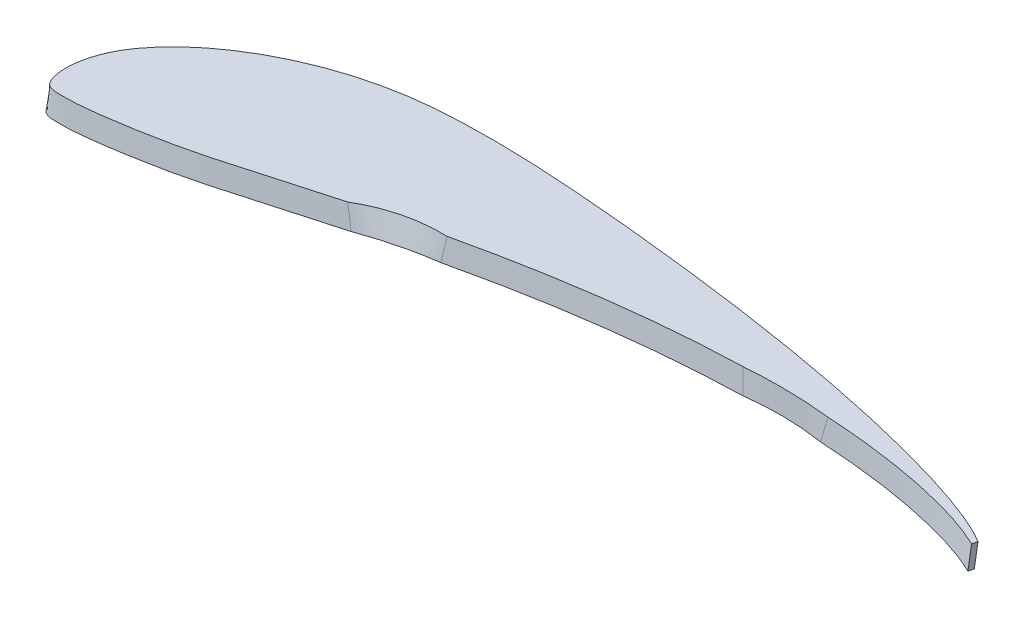
SolidWorks part; units mm, degrees
material "Elastyczna pianka poliuretanowa"
ref_plane "Płaszczyzna XY" through (0, 0, 0) normal (0, 0, 1) x (1, 0, 0)
ref_plane "Płaszczyzna XZ" through (0, 0, 0) normal (0, 1, 0) x (1, 0, 0)
ref_plane "Płaszczyzna YZ" through (0, 0, 0) normal (1, 0, 0) x (0, 0, -1)
sketch "Szkic1" plane through (0, 250.3609, 48.6652) normal (0, -0.9816, -0.1908) x (1, 0, 0)
  line L5 (-466.8113, 187.1171) -> (-472.9601, 210.044)
  line L6 (-486.589, 213.3723) -> (-503.6753, 194.6998)
  line L7 (-230.7182, 186.7181) -> (-231.6453, 188.6919)
  line L8 (-309.7858, 174.2461) -> (-322.6938, 197.9387)
  line L9 (-336.9508, 197.5316) -> (-348.183, 173.7817)
  line L12 (-230.7182, 186.7181) -> (-231.6453, 188.6919)
  arc A2 (-472.9601, 210.044) -> (-486.589, 213.3723) centre (-480.687, 207.9716) ccw
  arc A3 (-322.6938, 197.9387) -> (-336.9508, 197.5316) centre (-329.7188, 194.1114) ccw
  spline S0 degree 2 poles (-503.6753, 194.6998) (-486.1131, 186.6285) (-466.8113, 187.1171) knots 0 0 0 1 1 1
  spline S1 degree 2 poles (-348.183, 173.7817) (-328.9642, 172.457) (-309.7858, 174.2461) knots 0 0 0 1 1 1
  spline S3 degree 3 poles (961.1071, 2784.9605) (376.8727, 422.5481) (-14.446, 148.7113) (-387.9442, 175.9711) (-397.8476, 176.9178) (-417.6182, 179.2031) (-427.4849, 180.547) (-442.2607, 182.8262) (-447.1833, 183.629) (-952.66, 270.3189) (-1365.321, 774.2281) (-2411.9455, -1736.9733) knots -8.909011 -8.909011 -8.909011 -8.909011 0.25 0.25 0.5 0.5 0.75 0.75 0.875 0.875 13.61022 13.61022 13.61022 13.61022 only from (-348.183, 173.7817) to (-466.8113, 187.1171)
  spline S4 degree 3 poles (959.8042, 2726.3226) (76.9137, 59.3384) (-230.2357, 130.5607) (-542.8432, 203.7255) (-548.4338, 205.0452) (-556.8474, 206.8622) (-559.6562, 207.4413) (-565.2857, 208.5257) (-568.1069, 209.0278) (-573.7585, 209.9746) (-576.5885, 210.422) (-582.2554, 211.2742) (-585.0925, 211.6778) (-590.7758, 212.4276) (-593.6225, 212.7716) (-597.9026, 213.2244) (-599.3309, 213.3652) (-602.191, 213.626) (-603.6218, 213.7485) (-605.7691, 213.8905) (-606.485, 213.9308) (-607.9176, 213.9915) (-608.6343, 214.0112) (-610.0682, 214.0317) (-610.7855, 214.0332) (-612.2204, 214.0255) (-612.9379, 214.0186) (-614.3734, 213.9904) (-615.0944, 213.9596) (-616.1543, 213.8006) (-616.5044, 213.729) (-617.1963, 213.5371) (-617.5399, 213.4171) (-618.0259, 213.187) (-618.1836, 213.1018) (-618.4876, 212.9093) (-618.6352, 212.8007) (-618.9052, 212.5631) (-619.0284, 212.4336) (-619.2483, 212.1509) (-619.3465, 211.9965) (-619.6026, 211.5197) (-619.7252, 211.185) (-619.9226, 210.4991) (-619.9974, 210.1467) (-620.1221, 209.4394) (-620.17, 209.0839) (-620.2369, 208.3694) (-620.2561, 208.0094) (-620.2723, 206.9367) (-620.229, 206.2281) (-620.0607, 204.8205) (-619.9359, 204.1216) (-619.6245, 202.7312) (-619.4375, 202.0389) (-618.8007, 200.0009) (-618.2741, 198.6833) (-617.0617, 196.1121) (-616.374, 194.855) (-614.892, 192.4402) (-614.0928, 191.278) (-612.3839, 189.0391) (-611.4752, 187.9617) (-610.0457, 186.3971) (-609.558, 185.8842) (-608.5628, 184.8738) (-608.0543, 184.3755) (-606.5106, 182.909) (-605.4579, 181.9682) (-602.2469, 179.2284) (-600.0321, 177.5176) (-595.481, 174.2855) (-593.1452, 172.7635) (-588.3746, 169.874) (-585.94, 168.5062) (-580.9833, 165.9072) (-578.4601, 164.6778) (-574.6136, 162.9297) (-573.3212, 162.3628) (-570.7287, 161.2633) (-569.4273, 160.7298) (-565.5081, 159.1767) (-562.8751, 158.2045) (-557.5706, 156.3815) (-554.8991, 155.5304) (-549.5196, 153.9429) (-546.8116, 153.2068) (-542.7197, 152.1962) (-541.3507, 151.8751) (-538.6028, 151.2642) (-537.2227, 150.9739) (-533.0776, 150.1498) (-530.3121, 149.6617) (-524.7767, 148.8025) (-522.0069, 148.4327) (-516.4629, 147.8151) (-513.6887, 147.5661) (-505.3607, 146.9725) (-499.8012, 146.7859) (-488.6755, 146.5949) (-483.1089, 146.6035) (-471.9685, 146.8235) (-466.3949, 147.0264) (-455.2431, 147.5596) (-449.6626, 147.892) (-438.5168, 148.644) (-432.9494, 149.0616) (-421.8235, 149.9646) (-416.2651, 150.4506) (-405.1554, 151.4766) (-399.6041, 152.0165) (-382.9635, 153.7375) (-371.8875, 155.019) (-355.3036, 157.1703) (-349.7809, 157.9278) (-338.7475, 159.5325) (-333.2363, 160.3771) (-322.2269, 162.1645) (-316.7289, 163.1091) (-305.7473, 165.108) (-300.2637, 166.1621) (-292.0521, 167.8474) (-289.3172, 168.4267) (-283.8526, 169.625) (-281.1218, 170.2445) (-272.9497, 172.17) (-267.527, 173.5404) (-259.4493, 175.7889) (-256.7663, 176.5713) (-251.4259, 178.2236) (-248.7682, 179.0926) (-244.809, 180.4894) (-243.4939, 180.9709) (-240.875, 181.9727) (-239.5705, 182.4936) (-236.9854, 183.5816) (-235.7024, 184.1461) (-176.5919, 212.4643) (-159.7166, 327.3712) (-1332.0236, 2973.0527) knots -1.653404 -1.653404 -1.653404 -1.653404 0.0625 0.0625 0.09375 0.09375 0.109375 0.109375 0.125 0.125 0.140625 0.140625 0.15625 0.15625 0.171875 0.171875 0.179687 0.179687 0.1875 0.1875 0.191406 0.191406 0.195312 0.195312 0.199219 0.199219 0.203125 0.203125 0.207031 0.207031 0.208984 0.208984 0.210937 0.210937 0.211914 0.211914 0.212891 0.212891 0.213867 0.213867 0.214844 0.214844 0.216797 0.216797 0.21875 0.21875 0.220703 0.220703 0.222656 0.222656 0.226562 0.226562 0.230469 0.230469 0.234375 0.234375 0.242187 0.242187 0.25 0.25 0.257812 0.257812 0.265625 0.265625 0.269531 0.269531 0.273437 0.273437 0.28125 0.28125 0.296875 0.296875 0.3125 0.3125 0.328125 0.328125 0.34375 0.34375 0.351562 0.351562 0.359375 0.359375 0.375 0.375 0.390625 0.390625 0.40625 0.40625 0.414062 0.414062 0.421875 0.421875 0.4375 0.4375 0.453125 0.453125 0.46875 0.46875 0.5 0.5 0.53125 0.53125 0.5625 0.5625 0.59375 0.59375 0.625 0.625 0.65625 0.65625 0.6875 0.6875 0.75 0.75 0.78125 0.78125 0.8125 0.8125 0.84375 0.84375 0.875 0.875 0.890625 0.890625 0.90625 0.90625 0.9375 0.9375 0.953125 0.953125 0.96875 0.96875 0.976562 0.976562 0.984375 0.984375 0.992187 0.992187 1.349806 1.349806 1.349806 1.349806 only from (-503.6753, 194.6998) to (-230.7182, 186.7181)
  spline S5 degree 3 poles (-883.9723, 3110.6661) (-105.8224, 363.0378) (-153.1749, 218.5298) (-237.8412, 186.1719) (-239.414, 185.617) (-244.1644, 184.0531) (-247.3745, 183.1467) (-253.8516, 181.5134) (-257.1199, 180.7803) (-263.6577, 179.4539) (-266.9328, 178.8602) (-276.7736, 177.253) (-283.3547, 176.4124) (-650.9504, 139.297) (-1058.5112, 625.3856) (-1139.4136, -2554.4342) knots -3.267662 -3.267662 -3.267662 -3.267662 0.0625 0.0625 0.125 0.125 0.25 0.25 0.375 0.375 0.5 0.5 0.75 0.75 14.431103 14.431103 14.431103 14.431103 only from (-231.6453, 188.6919) to (-309.7858, 174.2461)
  spline S6 degree 3 poles (-348.183, 173.7817) (-358.1517, 174.022) (-368.0963, 174.5225) (-387.9442, 175.9711) (-397.8476, 176.9178) (-417.6182, 179.2031) (-427.4849, 180.547) (-442.2607, 182.8262) (-447.1833, 183.629) (-457.0097, 185.3143) (-461.9144, 186.1972) (-466.8113, 187.1171) knots 0 0 0 0 0.25 0.25 0.5 0.5 0.75 0.75 0.875 0.875 1 1 1 1
  spline S7 degree 3 poles (-503.6753, 194.6998) (-514.8862, 197.1832) (-526.0691, 199.7996) (-542.8432, 203.7255) (-548.4338, 205.0452) (-556.8474, 206.8622) (-559.6562, 207.4413) (-565.2857, 208.5257) (-568.1069, 209.0278) (-573.7585, 209.9746) (-576.5885, 210.422) (-582.2554, 211.2742) (-585.0925, 211.6778) (-590.7758, 212.4276) (-593.6225, 212.7716) (-597.9026, 213.2244) (-599.3309, 213.3652) (-602.191, 213.626) (-603.6218, 213.7485) (-605.7691, 213.8905) (-606.485, 213.9308) (-607.9176, 213.9915) (-608.6343, 214.0112) (-610.0682, 214.0317) (-610.7855, 214.0332) (-612.2204, 214.0255) (-612.9379, 214.0186) (-614.3734, 213.9904) (-615.0944, 213.9596) (-616.1543, 213.8006) (-616.5044, 213.729) (-617.1963, 213.5371) (-617.5399, 213.4171) (-618.0259, 213.187) (-618.1836, 213.1018) (-618.4876, 212.9093) (-618.6352, 212.8007) (-618.9052, 212.5631) (-619.0284, 212.4336) (-619.2483, 212.1509) (-619.3465, 211.9965) (-619.6026, 211.5197) (-619.7252, 211.185) (-619.9226, 210.4991) (-619.9974, 210.1467) (-620.1221, 209.4394) (-620.17, 209.0839) (-620.2369, 208.3694) (-620.2561, 208.0094) (-620.2723, 206.9367) (-620.229, 206.2281) (-620.0607, 204.8205) (-619.9359, 204.1216) (-619.6245, 202.7312) (-619.4375, 202.0389) (-618.8007, 200.0009) (-618.2741, 198.6833) (-617.0617, 196.1121) (-616.374, 194.855) (-614.892, 192.4402) (-614.0928, 191.278) (-612.3839, 189.0391) (-611.4752, 187.9617) (-610.0457, 186.3971) (-609.558, 185.8842) (-608.5628, 184.8738) (-608.0543, 184.3755) (-606.5106, 182.909) (-605.4579, 181.9682) (-602.2469, 179.2284) (-600.0321, 177.5176) (-595.481, 174.2855) (-593.1452, 172.7635) (-588.3746, 169.874) (-585.94, 168.5062) (-580.9833, 165.9072) (-578.4601, 164.6778) (-574.6136, 162.9297) (-573.3212, 162.3628) (-570.7287, 161.2633) (-569.4273, 160.7298) (-565.5081, 159.1767) (-562.8751, 158.2045) (-557.5706, 156.3815) (-554.8991, 155.5304) (-549.5196, 153.9429) (-546.8116, 153.2068) (-542.7197, 152.1962) (-541.3507, 151.8751) (-538.6028, 151.2642) (-537.2227, 150.9739) (-533.0776, 150.1498) (-530.3121, 149.6617) (-524.7767, 148.8025) (-522.0069, 148.4327) (-516.4629, 147.8151) (-513.6887, 147.5661) (-505.3607, 146.9725) (-499.8012, 146.7859) (-488.6755, 146.5949) (-483.1089, 146.6035) (-471.9685, 146.8235) (-466.3949, 147.0264) (-455.2431, 147.5596) (-449.6626, 147.892) (-438.5168, 148.644) (-432.9494, 149.0616) (-421.8235, 149.9646) (-416.2651, 150.4506) (-405.1554, 151.4766) (-399.6041, 152.0165) (-382.9635, 153.7375) (-371.8875, 155.019) (-355.3036, 157.1703) (-349.7809, 157.9278) (-338.7475, 159.5325) (-333.2363, 160.3771) (-322.2269, 162.1645) (-316.7289, 163.1091) (-305.7473, 165.108) (-300.2637, 166.1621) (-292.0521, 167.8474) (-289.3172, 168.4267) (-283.8526, 169.625) (-281.1218, 170.2445) (-272.9497, 172.17) (-267.527, 173.5404) (-259.4493, 175.7889) (-256.7663, 176.5713) (-251.4259, 178.2236) (-248.7682, 179.0926) (-244.809, 180.4894) (-243.4939, 180.9709) (-240.875, 181.9727) (-239.5705, 182.4936) (-236.9854, 183.5816) (-235.7024, 184.1461) (-233.175, 185.3569) (-231.9308, 186.004) (-230.7182, 186.7181) knots 0 0 0 0 0.0625 0.0625 0.09375 0.09375 0.109375 0.109375 0.125 0.125 0.140625 0.140625 0.15625 0.15625 0.171875 0.171875 0.179687 0.179687 0.1875 0.1875 0.191406 0.191406 0.195312 0.195312 0.199219 0.199219 0.203125 0.203125 0.207031 0.207031 0.208984 0.208984 0.210937 0.210937 0.211914 0.211914 0.212891 0.212891 0.213867 0.213867 0.214844 0.214844 0.216797 0.216797 0.21875 0.21875 0.220703 0.220703 0.222656 0.222656 0.226562 0.226562 0.230469 0.230469 0.234375 0.234375 0.242187 0.242187 0.25 0.25 0.257812 0.257812 0.265625 0.265625 0.269531 0.269531 0.273437 0.273437 0.28125 0.28125 0.296875 0.296875 0.3125 0.3125 0.328125 0.328125 0.34375 0.34375 0.351562 0.351562 0.359375 0.359375 0.375 0.375 0.390625 0.390625 0.40625 0.40625 0.414062 0.414062 0.421875 0.421875 0.4375 0.4375 0.453125 0.453125 0.46875 0.46875 0.5 0.5 0.53125 0.53125 0.5625 0.5625 0.59375 0.59375 0.625 0.625 0.65625 0.65625 0.6875 0.6875 0.75 0.75 0.78125 0.78125 0.8125 0.8125 0.84375 0.84375 0.875 0.875 0.890625 0.890625 0.90625 0.90625 0.9375 0.9375 0.953125 0.953125 0.96875 0.96875 0.976562 0.976562 0.984375 0.984375 0.992187 0.992187 1 1 1 1
  spline S8 degree 3 poles (-231.6453, 188.6919) (-233.1746, 188) (-234.7218, 187.3641) (-237.8412, 186.1719) (-239.414, 185.617) (-244.1644, 184.0531) (-247.3745, 183.1467) (-253.8516, 181.5134) (-257.1199, 180.7803) (-263.6577, 179.4539) (-266.9328, 178.8602) (-276.7736, 177.253) (-283.3547, 176.4124) (-296.5481, 175.0803) (-303.1603, 174.5888) (-309.7858, 174.2461) knots 0 0 0 0 0.0625 0.0625 0.125 0.125 0.25 0.25 0.375 0.375 0.5 0.5 0.75 0.75 1 1 1 1
  dimension "D1" = 0
sketch "Szkic2" plane through (0, 241.3299, 46.9098) normal (0, 0.9816, 0.1908) x (1, 0, 0)
  line L5 (-346.5635, -177.2061) -> (-336.9508, -197.5316)
  line L6 (-322.6938, -197.9387) -> (-311.6218, -177.6162)
  line L7 (-231.6462, -192.1508) -> (-230.7191, -190.1773)
  line L8 (-501.0426, -197.5769) -> (-486.589, -213.3723)
  line L9 (-472.9601, -210.044) -> (-467.7883, -190.76)
  line L12 (-231.6462, -192.1508) -> (-230.7191, -190.1773)
  arc A2 (-336.9508, -197.5316) -> (-322.6938, -197.9387) centre (-329.7188, -194.1114) ccw
  arc A3 (-486.589, -213.3723) -> (-472.9601, -210.044) centre (-480.687, -207.9716) ccw
  spline S0 degree 2 poles (-501.0426, -197.5769) (-484.7064, -192.7356) (-467.7883, -190.76) knots 0 0 0 1 1 1
  spline S1 degree 2 poles (-346.5635, -177.2061) (-329.0621, -175.2488) (-311.6218, -177.6162) knots 0 0 0 1 1 1
  spline S3 degree 3 poles (-2391.9418, 1769.2386) (-1351.11, -759.7133) (-944.2235, -272.689) (-447.74, -187.1805) (-442.7129, -186.3578) (-427.6223, -184.0241) (-417.543, -182.6508) (-397.3413, -180.324) (-387.2194, -179.3651) (-372.0005, -178.2765) (-366.9215, -177.9724) (-59.4889, -163.4322) (280.3775, -373.7296) (-2743.4147, -1900.722) knots -12.116321 -12.116321 -12.116321 -12.116321 0.125 0.125 0.25 0.25 0.5 0.5 0.75 0.75 0.875 0.875 8.306481 8.306481 8.306481 8.306481 only from (-467.7883, -190.76) to (-346.5635, -177.2061)
  spline S4 degree 3 poles (-1192.0704, 2530.1655) (-1065.4952, -639.2296) (-658.0587, -143.4351) (-284.5996, -179.7248) (-277.8676, -180.5599) (-267.797, -182.1697) (-264.4447, -182.7664) (-259.4246, -183.769) (-257.7526, -184.1214) (-254.4117, -184.8663) (-252.7433, -185.2585) (-247.7636, -186.4999) (-244.473, -187.4191) (-239.6047, -189.0104) (-237.9931, -189.5759) (-152.8386, -221.9932) (-105.2977, -366.946) (-885.8816, -3113.4705) knots -13.340567 -13.340567 -13.340567 -13.340567 0.25 0.25 0.5 0.5 0.625 0.625 0.6875 0.6875 0.75 0.75 0.875 0.875 0.9375 0.9375 4.205555 4.205555 4.205555 4.205555 only from (-311.6218, -177.6162) to (-231.6462, -192.1508)
  spline S5 degree 3 poles (-1667.1028, -2818.5437) (-146.9055, -333.2023) (-177.4327, -215.465) (-235.7553, -187.582) (-237.0435, -187.0164) (-240.9306, -185.3834) (-243.5556, -184.3908) (-248.8479, -182.5265) (-251.5154, -181.6556) (-256.8801, -179.9984) (-259.5776, -179.2131) (-264.9955, -177.7078) (-267.7169, -176.9877) (-273.1732, -175.6001) (-275.9055, -174.9339) (-284.1129, -173.0045) (-289.5984, -171.8105) (-300.5904, -169.5602) (-306.0969, -168.5043) (-317.1264, -166.502) (-322.6495, -165.5559) (-339.242, -162.8707) (-350.3327, -161.2725) (-372.5633, -158.4009) (-383.7018, -157.1184) (-400.4402, -155.3973) (-406.0248, -154.8572) (-417.2021, -153.8311) (-422.7965, -153.3456) (-433.9862, -152.446) (-439.5814, -152.0308) (-450.7728, -151.2874) (-456.369, -150.9616) (-467.563, -150.4446) (-473.1607, -150.2514) (-484.3582, -150.0585) (-489.9582, -150.0667) (-501.1604, -150.2911) (-506.7627, -150.5044) (-515.1698, -151.1586) (-517.9728, -151.4304) (-523.5802, -152.1007) (-526.3878, -152.4995) (-534.7407, -153.8667) (-540.2408, -155.0033) (-548.3749, -157.0894) (-551.0677, -157.8458) (-556.4186, -159.4725) (-559.0764, -160.3437) (-564.3549, -162.2081) (-566.9755, -163.2015) (-572.1778, -165.3161) (-574.76, -166.4359) (-579.879, -168.8239) (-582.4215, -170.0967) (-587.4, -172.7806) (-589.8423, -174.1921) (-597.0062, -178.6685) (-601.5674, -181.9712) (-606.8662, -186.6968) (-607.9073, -187.675) (-609.9066, -189.6896) (-610.8675, -190.7281) (-612.693, -192.8826) (-613.5572, -193.9988) (-614.7672, -195.7426) (-615.1565, -196.3351) (-615.9062, -197.5435) (-616.2672, -198.1604) (-617.3012, -200.0402) (-617.9189, -201.3214) (-618.9757, -203.9529) (-619.4154, -205.3032) (-619.901, -207.3961) (-620.0336, -208.1038) (-620.216, -209.5188) (-620.2918, -210.5842) (-620.248, -211.6578) (-620.1896, -212.3755) (-620.1458, -212.734) (-620.0297, -213.4422) (-619.9597, -213.7937) (-619.822, -214.3136) (-619.7703, -214.4856) (-619.6499, -214.8258) (-619.5807, -214.9953) (-619.4218, -215.3205) (-619.3321, -215.4767) (-619.1259, -215.7721) (-619.0071, -215.9122) (-618.6148, -216.2918) (-618.3125, -216.492) (-617.6633, -216.8221) (-617.326, -216.9474) (-616.6364, -217.1515) (-616.283, -217.2297) (-615.2099, -217.4043) (-614.4867, -217.4399) (-613.4013, -217.4639) (-613.0398, -217.468) (-612.3167, -217.4768) (-611.9552, -217.4803) (-610.1482, -217.4911) (-608.7043, -217.4773) (-605.8228, -217.3573) (-604.3848, -217.2573) (-601.5114, -217.0217) (-600.0758, -216.8894) (-597.2057, -216.6069) (-595.7713, -216.4552) (-591.4705, -215.9695) (-588.6054, -215.6043) (-582.8872, -214.82) (-580.0329, -214.4016) (-574.3326, -213.5197) (-571.4861, -213.0585) (-565.8046, -212.0736) (-562.9702, -211.5463) (-557.3151, -210.4166) (-554.4938, -209.8175) (-548.86, -208.5717) (-546.0473, -207.9254) (-540.4248, -206.6174) (-537.6147, -205.9576) (-227.5539, -133.4405) (81.3517, -69.4561) (962.8198, -2729.4203) knots -0.342252 -0.342252 -0.342252 -0.342252 0.007812 0.007812 0.015625 0.015625 0.03125 0.03125 0.046875 0.046875 0.0625 0.0625 0.078125 0.078125 0.09375 0.09375 0.125 0.125 0.15625 0.15625 0.1875 0.1875 0.25 0.25 0.3125 0.3125 0.34375 0.34375 0.375 0.375 0.40625 0.40625 0.4375 0.4375 0.46875 0.46875 0.5 0.5 0.53125 0.53125 0.546875 0.546875 0.5625 0.5625 0.59375 0.59375 0.609375 0.609375 0.625 0.625 0.640625 0.640625 0.65625 0.65625 0.671875 0.671875 0.6875 0.6875 0.71875 0.71875 0.726562 0.726562 0.734375 0.734375 0.742187 0.742187 0.746094 0.746094 0.75 0.75 0.757812 0.757812 0.765625 0.765625 0.769531 0.769531 0.773437 0.775391 0.775391 0.777344 0.777344 0.779297 0.779297 0.780273 0.780273 0.78125 0.78125 0.782227 0.782227 0.783203 0.783203 0.785156 0.785156 0.787109 0.787109 0.789062 0.789062 0.792969 0.792969 0.794922 0.794922 0.796875 0.796875 0.804687 0.804687 0.8125 0.8125 0.820312 0.820312 0.828125 0.828125 0.84375 0.84375 0.859375 0.859375 0.875 0.875 0.890625 0.890625 0.90625 0.90625 0.921875 0.921875 0.9375 0.9375 2.645614 2.645614 2.645614 2.645614 only from (-230.7191, -190.1773) to (-501.0426, -197.5769)
  spline S6 degree 3 poles (-467.7883, -190.76) (-462.7867, -189.8154) (-457.777, -188.9092) (-447.74, -187.1805) (-442.7129, -186.3578) (-427.6223, -184.0241) (-417.543, -182.6508) (-397.3413, -180.324) (-387.2194, -179.3651) (-372.0005, -178.2765) (-366.9215, -177.9724) (-356.7503, -177.4913) (-351.6541, -177.3143) (-346.5635, -177.2061) knots 0 0 0 0 0.125 0.125 0.25 0.25 0.5 0.5 0.75 0.75 0.875 0.875 1 1 1 1
  spline S7 degree 3 poles (-311.6218, -177.6162) (-304.8505, -177.9381) (-298.091, -178.4138) (-284.5996, -179.7248) (-277.8676, -180.5599) (-267.797, -182.1697) (-264.4447, -182.7664) (-259.4246, -183.769) (-257.7526, -184.1214) (-254.4117, -184.8663) (-252.7433, -185.2585) (-247.7636, -186.4999) (-244.473, -187.4191) (-239.6047, -189.0104) (-237.9931, -189.5759) (-234.7971, -190.7926) (-233.2123, -191.4423) (-231.6462, -192.1508) knots 0 0 0 0 0.25 0.25 0.5 0.5 0.625 0.625 0.6875 0.6875 0.75 0.75 0.875 0.875 0.9375 0.9375 1 1 1 1
  spline S8 degree 3 poles (-230.7191, -190.1773) (-231.9489, -189.4531) (-233.2089, -188.7994) (-235.7553, -187.582) (-237.0435, -187.0164) (-240.9306, -185.3834) (-243.5556, -184.3908) (-248.8479, -182.5265) (-251.5154, -181.6556) (-256.8801, -179.9984) (-259.5776, -179.2131) (-264.9955, -177.7078) (-267.7169, -176.9877) (-273.1732, -175.6001) (-275.9055, -174.9339) (-284.1129, -173.0045) (-289.5984, -171.8105) (-300.5904, -169.5602) (-306.0969, -168.5043) (-317.1264, -166.502) (-322.6495, -165.5559) (-339.242, -162.8707) (-350.3327, -161.2725) (-372.5633, -158.4009) (-383.7018, -157.1184) (-400.4402, -155.3973) (-406.0248, -154.8572) (-417.2021, -153.8311) (-422.7965, -153.3456) (-433.9862, -152.446) (-439.5814, -152.0308) (-450.7728, -151.2874) (-456.369, -150.9616) (-467.563, -150.4446) (-473.1607, -150.2514) (-484.3582, -150.0585) (-489.9582, -150.0667) (-501.1604, -150.2911) (-506.7627, -150.5044) (-515.1698, -151.1586) (-517.9728, -151.4304) (-523.5802, -152.1007) (-526.3878, -152.4995) (-534.7407, -153.8667) (-540.2408, -155.0033) (-548.3749, -157.0894) (-551.0677, -157.8458) (-556.4186, -159.4725) (-559.0764, -160.3437) (-564.3549, -162.2081) (-566.9755, -163.2015) (-572.1778, -165.3161) (-574.76, -166.4359) (-579.879, -168.8239) (-582.4215, -170.0967) (-587.4, -172.7806) (-589.8423, -174.1921) (-597.0062, -178.6685) (-601.5674, -181.9712) (-606.8662, -186.6968) (-607.9073, -187.675) (-609.9066, -189.6896) (-610.8675, -190.7281) (-612.693, -192.8826) (-613.5572, -193.9988) (-614.7672, -195.7426) (-615.1565, -196.3351) (-615.9062, -197.5435) (-616.2672, -198.1604) (-617.3012, -200.0402) (-617.9189, -201.3214) (-618.9757, -203.9529) (-619.4154, -205.3032) (-619.901, -207.3961) (-620.0336, -208.1038) (-620.216, -209.5188) (-620.2918, -210.5842) (-620.248, -211.6578) (-620.1896, -212.3755) (-620.1458, -212.734) (-620.0297, -213.4422) (-619.9597, -213.7937) (-619.822, -214.3136) (-619.7703, -214.4856) (-619.6499, -214.8258) (-619.5807, -214.9953) (-619.4218, -215.3205) (-619.3321, -215.4767) (-619.1259, -215.7721) (-619.0071, -215.9122) (-618.6148, -216.2918) (-618.3125, -216.492) (-617.6633, -216.8221) (-617.326, -216.9474) (-616.6364, -217.1515) (-616.283, -217.2297) (-615.2099, -217.4043) (-614.4867, -217.4399) (-613.4013, -217.4639) (-613.0398, -217.468) (-612.3167, -217.4768) (-611.9552, -217.4803) (-610.1482, -217.4911) (-608.7043, -217.4773) (-605.8228, -217.3573) (-604.3848, -217.2573) (-601.5114, -217.0217) (-600.0758, -216.8894) (-597.2057, -216.6069) (-595.7713, -216.4552) (-591.4705, -215.9695) (-588.6054, -215.6043) (-582.8872, -214.82) (-580.0329, -214.4016) (-574.3326, -213.5197) (-571.4861, -213.0585) (-565.8046, -212.0736) (-562.9702, -211.5463) (-557.3151, -210.4166) (-554.4938, -209.8175) (-548.86, -208.5717) (-546.0473, -207.9254) (-540.4248, -206.6174) (-537.6147, -205.9576) (-523.5619, -202.6709) (-512.3173, -200.0521) (-501.0426, -197.5769) knots 0 0 0 0 0.007812 0.007812 0.015625 0.015625 0.03125 0.03125 0.046875 0.046875 0.0625 0.0625 0.078125 0.078125 0.09375 0.09375 0.125 0.125 0.15625 0.15625 0.1875 0.1875 0.25 0.25 0.3125 0.3125 0.34375 0.34375 0.375 0.375 0.40625 0.40625 0.4375 0.4375 0.46875 0.46875 0.5 0.5 0.53125 0.53125 0.546875 0.546875 0.5625 0.5625 0.59375 0.59375 0.609375 0.609375 0.625 0.625 0.640625 0.640625 0.65625 0.65625 0.671875 0.671875 0.6875 0.6875 0.71875 0.71875 0.726562 0.726562 0.734375 0.734375 0.742187 0.742187 0.746094 0.746094 0.75 0.75 0.757812 0.757812 0.765625 0.765625 0.769531 0.769531 0.773437 0.775391 0.775391 0.777344 0.777344 0.779297 0.779297 0.780273 0.780273 0.78125 0.78125 0.782227 0.782227 0.783203 0.783203 0.785156 0.785156 0.787109 0.787109 0.789062 0.789062 0.792969 0.792969 0.794922 0.794922 0.796875 0.796875 0.804687 0.804687 0.8125 0.8125 0.820312 0.820312 0.828125 0.828125 0.84375 0.84375 0.859375 0.859375 0.875 0.875 0.890625 0.890625 0.90625 0.90625 0.921875 0.921875 0.9375 0.9375 1 1 1 1
  dimension "D1" = 0
loft "Wyciągnięcie po profilach1" add profiles "Szkic1", "Szkic2"
